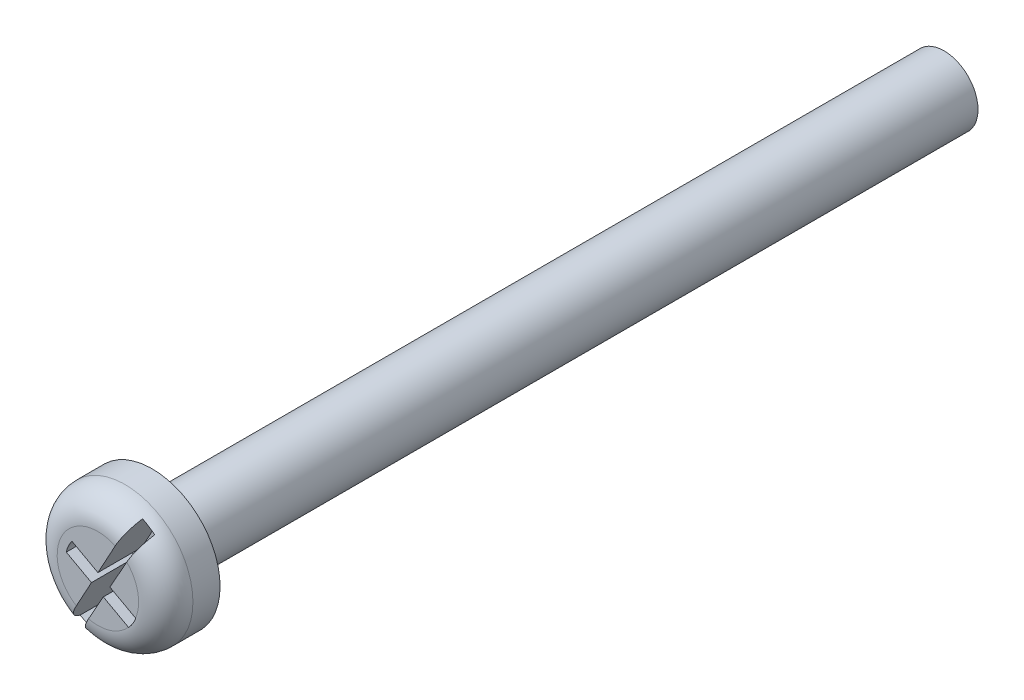
SolidWorks part; units mm, degrees
material "Stop odlewniczy stali"
ref_plane "Płaszczyzna przednia" through (0, 0, 0) normal (0, 0, 1) x (1, 0, 0)
ref_plane "Płaszczyzna górna" through (0, 0, 0) normal (0, 1, 0) x (1, 0, 0)
ref_plane "Płaszczyzna prawa" through (0, 0, 0) normal (1, 0, 0) x (0, 0, -1)
sketch "Szkic1" plane through (0, 0, 0) normal (0, 0, 1) x (1, 0, 0)
  circle A0 centre (-1.8605, 2.7321) radius 3
  dimension "D1" = 6
extrude "Dodanie-wyciągnięcie2" add sketch "Szkic1" along normal blind 2.4
sketch "Szkic2" plane through (0, 0, 0) normal (0, 0, -1) x (-1, 0, 0)
  circle A0 centre (1.8605, 2.7321) radius 1.5
extrude "Dodanie-wyciągnięcie3" add sketch "Szkic2" along normal blind 35
fillet "Zaokrąglenie2" radius 1.2 1 edges at (1.1395, 2.7321, 2.4)
sketch "Szkic3" plane through (0, 0, 2.4) normal (0, 0, 1) x (1, 0, 0)
  line L0 (-1.8595, 2.9591) -> (-0.5756, 5.3165)
  line L1 (-1.8595, 2.9591) -> (-3.0095, 3.5874)
  line L2 (-3.3345, 0.2508) -> (-2.1451, 2.4347)
  line L3 (-2.8199, 0.0102) -> (-1.6213, 2.1486)
  line L4 (-0.184, 2.0436) -> (-1.3294, 2.6694)
  line L5 (-0.4992, 1.5357) -> (-1.6213, 2.1486)
  line L6 (-1.3294, 2.6694) -> (-0.0393, 4.9711)
  line L7 (-2.1451, 2.4347) -> (-3.2587, 3.0429)
  arc A2 (-3.0095, 3.5874) -> (-3.2587, 3.0429) centre (-1.8605, 2.7321) ccw
  arc A3 (-0.0393, 4.9711) -> (-0.5756, 5.3165) centre (-1.8605, 2.7321) ccw
  arc A4 (-3.3345, 0.2508) -> (-2.8199, 0.0102) centre (-1.8605, 2.7321) ccw
  arc A6 (-0.4992, 1.5357) -> (-0.184, 2.0436) centre (-1.8605, 2.7321) ccw
extrude "Wytnij-wyciągnięcie1" cut sketch "Szkic3" against normal blind 1.94
